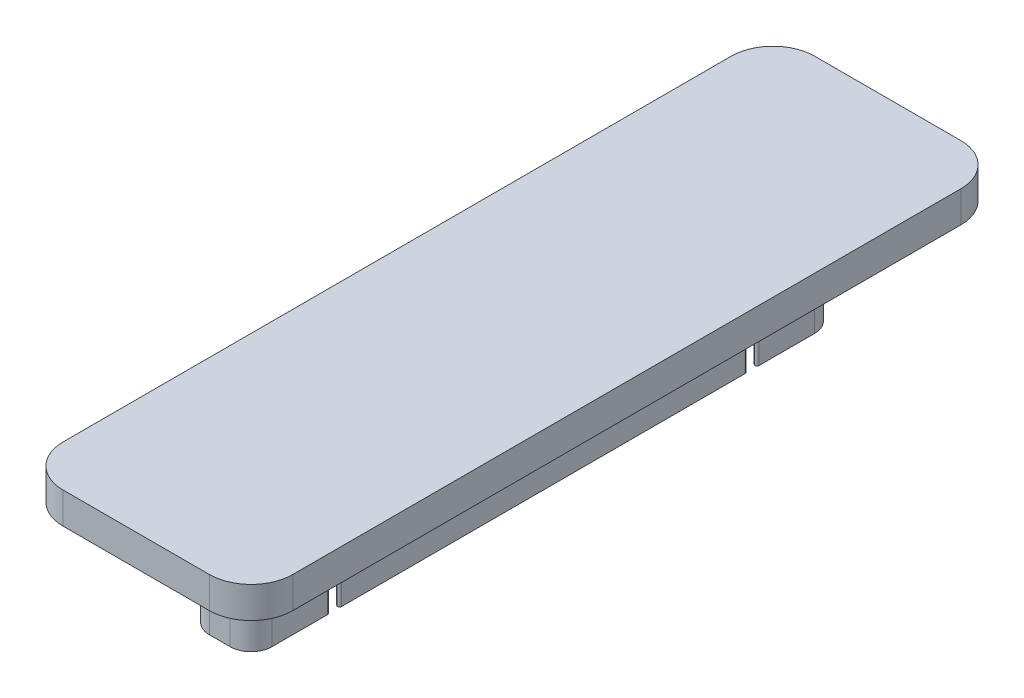
SolidWorks part; units mm, degrees
ref_plane "Спереди" through (0, 0, 0) normal (0, 0, 1) x (1, 0, 0)
ref_plane "Сверху" through (0, 0, 0) normal (0, 1, 0) x (1, 0, 0)
ref_plane "Справа" through (0, 0, 0) normal (1, 0, 0) x (0, 0, -1)
sketch "Эскиз1" plane through (0, 0, 0) normal (0, 1, 0) x (1, 0, 0)
  line L1 (1.5, 14) -> (-1.5, 14)
  line L2 (1.5, 14) -> (1.5, -14)
  line L3 (1.5, -14) -> (-1.5, -14)
  line L4 (-1.5, 14) -> (-1.5, -14)
  line L5 (1.5, 14) -> (-1.5, -14) construction
  line L6 (1.5, -14) -> (-1.5, 14) construction
  point P1 (0, 0)
  dimension "D1" = 28
  dimension "D2" = 3
extrude "Бобышка-Вытянуть1" add sketch "Эскиз1" along normal blind 10
sketch "Эскиз2" plane through (0, 0, 0) normal (0, -1, 0) x (1, 0, 0)
  line L1 (-5.5, -12) -> (5.5, -12)
  line L2 (-5.5, -12) -> (-5.5, 12)
  line L3 (-5.5, 12) -> (5.5, 12)
  line L4 (5.5, -12) -> (5.5, 12)
  line L5 (-5.5, -12) -> (5.5, 12) construction
  line L6 (-5.5, 12) -> (5.5, -12) construction
  point P0 (0, 0)
  dimension "D1" = 24
  dimension "D2" = 11
extrude "Бобышка-Вытянуть2" add sketch "Эскиз2" along normal blind 1.5
fillet "Скругление1" radius 1 4 edges at (1.5, 5, -14) (-1.5, 5, -14) (1.5, 5, 14) (-1.5, 5, 14)
sketch "Эскиз3" plane through (0, 10, 0) normal (0, 1, 0) x (1, 0, 0)
  line L1 (5.5, -18) -> (-5.5, -18)
  line L2 (5.5, -18) -> (5.5, 18)
  line L3 (5.5, 18) -> (-5.5, 18)
  line L4 (-5.5, -18) -> (-5.5, 18)
  line L5 (5.5, -18) -> (-5.5, 18) construction
  line L6 (5.5, 18) -> (-5.5, -18) construction
  point P0 (0, 0)
  dimension "D1" = 36
  dimension "D2" = 11
extrude "Бобышка-Вытянуть3" add sketch "Эскиз3" along normal blind 1.5
fillet "Скругление3" radius 1 4 edges at (5.5, -0.75, 12) (-5.5, -0.75, 12) (5.5, -0.75, -12) (-5.5, -0.75, -12)
sketch "Эскиз5" plane through (0, -1.5, 0) normal (0, -1, 0) x (-1, 0, 0)
  line L0 (5.5, 18) -> (5.5, -18) construction
  line L1 (-5.5, 15) -> (5.5, 15)
  line L2 (-5.5, 15) -> (-5.5, -15)
  line L3 (-5.5, -15) -> (5.5, -15)
  line L4 (5.5, 15) -> (5.5, -15)
  line L5 (-5.5, 15) -> (5.5, -15) construction
  line L6 (-5.5, -15) -> (5.5, 15) construction
  point P0 (0, 0)
  dimension "D1" = 30
extrude "Вырез-Вытянуть1" cut sketch "Эскиз5" against normal blind 6.5
sketch "Эскиз6" plane through (0, 5, 0) normal (0, -1, 0) x (1, 0, 0)
  line L38 (-1.6, -10) -> (-0.3604, -8.7604)
  line L39 (0.3604, -8.7604) -> (1.6, -10)
  line L40 (1.6, -10) -> (0.3604, -11.2396)
  line L41 (-0.3604, -11.2396) -> (-1.6, -10)
  line L42 (-0.3604, -8.7604) -> (-0.3604, -8.2508)
  line L43 (0.3604, -8.7604) -> (0.3604, -8.2508)
  line L44 (-0.3604, -8.2508) -> (0.3604, -8.2508)
  line L45 (-0.3604, -11.2396) -> (-0.3604, -11.7881)
  line L46 (0.3604, -11.2396) -> (0.3604, -11.7881)
  line L47 (-0.3604, -11.7881) -> (0.3604, -11.7881)
  line L48 (3.575, 0) -> (-3.575, 0) construction
  line L49 (-0.3604, 11.7881) -> (0.3604, 11.7881)
  line L50 (0.3604, 11.2396) -> (0.3604, 11.7881)
  line L51 (-0.3604, 11.2396) -> (-0.3604, 11.7881)
  line L52 (-0.3604, 8.2508) -> (0.3604, 8.2508)
  line L53 (0.3604, 8.7604) -> (0.3604, 8.2508)
  line L54 (-0.3604, 8.7604) -> (-0.3604, 8.2508)
  line L55 (-0.3604, 11.2396) -> (-1.6, 10)
  line L56 (1.6, 10) -> (0.3604, 11.2396)
  line L57 (0.3604, 8.7604) -> (1.6, 10)
  line L58 (-1.6, 10) -> (-0.3604, 8.7604)
extrude "Вырез-Вытянуть2" cut sketch "Эскиз6" against normal blind 3
fillet "Скругление4" radius 2 4 edges at (-5.5, 10.75, 18) (5.5, 10.75, 18) (5.5, 10.75, -18) (-5.5, 10.75, -18)
fillet "Скругление5" radius 0.1 8 edges at (-1.5, 6.5, -10.1) (-1.5, 6.5, -9.9) (1.5, 6.5, -10.1) (1.5, 6.5, -9.9) (-1.5, 6.5, 10.1) (-1.5, 6.5, 9.9) (1.5, 6.5, 9.9) (1.5, 6.5, 10.1)
